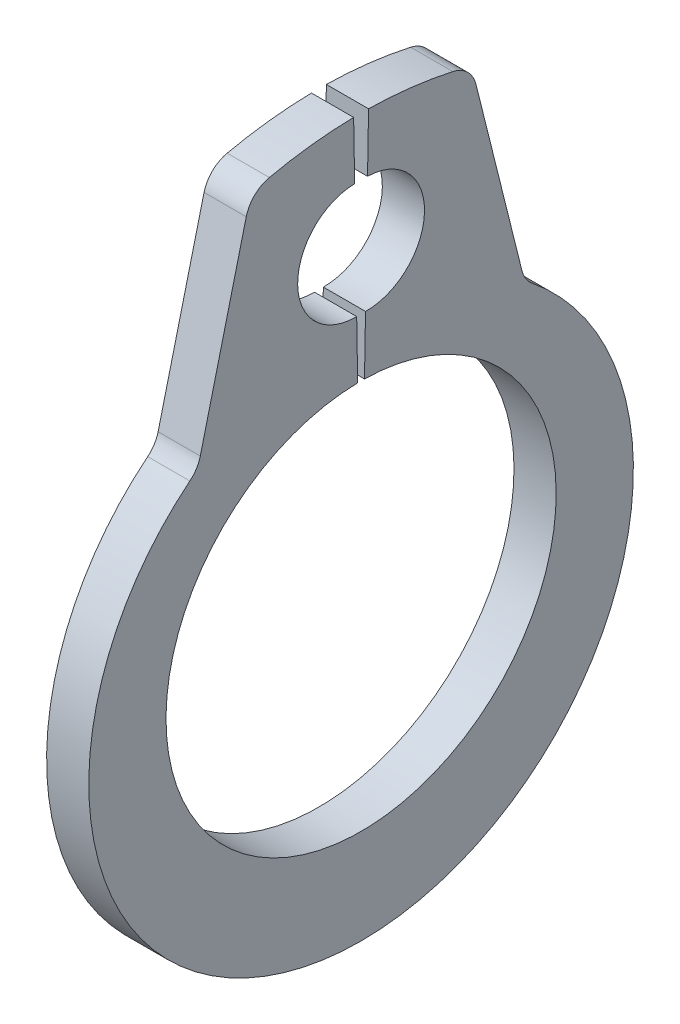
SolidWorks part; units mm, degrees
material "Cast Carbon Steel"
ref_plane "Front" through (0, 0, 0) normal (0, 0, 1) x (1, 0, 0)
ref_plane "Top" through (0, 0, 0) normal (0, 1, 0) x (1, 0, 0)
ref_plane "Right" through (0, 0, 0) normal (1, 0, 0) x (0, 0, -1)
sketch "Sketch1" plane through (0, 0, 0) normal (1, 0, 0) x (0, 0, -1)
  line L0 (0, 0) -> (0, 1.85) construction
  line L1 (-0.0323, 1.8497) -> (-0.0707, 4.0494) construction
  line L2 (-0.0707, 4.0494) -> (-1.0167, 4.0329) construction
  line L3 (-1.0167, 4.0329) -> (-1.549, 1.8982) construction
  line L4 (0.0707, 4.0494) -> (0.0323, 1.8497) construction
  line L5 (0.0707, 4.0494) -> (1.0167, 4.0329) construction
  line L6 (1.0167, 4.0329) -> (1.549, 1.8982) construction
  line L7 (-1.549, 1.8982) -> (-1.1696, 1.4333) construction
  line L8 (1.549, 1.8982) -> (1.1696, 1.4333) construction
  line L9 (0, -1.85) -> (0, -2.75) construction
  line L10 (-1.0167, 4.0329) -> (-0.0323, 1.8497) construction
  line L11 (0.0323, 1.8497) -> (0.0419, 2.3996)
  line L12 (0, 1.85) -> (0, 4.05) construction
  line L13 (1.0468, 3.9124) -> (1.549, 1.8982)
  line L14 (-1.0468, 3.9124) -> (-1.549, 1.8982)
  line L16 (0.0611, 3.4995) -> (0.0707, 4.0494)
  line L17 (-0.0611, 3.4995) -> (-0.0707, 4.0494)
  line L18 (-0.0419, 2.3996) -> (-0.0323, 1.8497)
  circle A0 centre (0, 0) radius 1.85 construction
  arc A1 (-0.0323, 1.8497) -> (0.0323, 1.8497) centre (0, 0) ccw
  circle A2 centre (0, -0.1678) radius 2.5822 construction
  arc A3 (0.0611, 3.4995) -> (0.0419, 2.3996) centre (0.0515, 2.9496) cw
  arc A4 (-0.0419, 2.3996) -> (-0.0611, 3.4995) centre (-0.0515, 2.9496) cw
  arc A6 (-1.549, 1.8982) -> (1.549, 1.8982) centre (0, -0.1678) ccw
  arc A7 (0.0707, 4.0494) -> (1.0468, 3.9124) centre (0, 0) cw
  arc A8 (-0.0707, 4.0494) -> (-1.0468, 3.9124) centre (0, 0) ccw
  dimension "D1" = 75
  dimension "A" = 3.7
  dimension "D2" = 1.1
  dimension "Smin" = 0.6
  dimension "Smax" = 0.9
  dimension "H" = 2.2
  dimension "Angle" = 1
extrude "Extrude1" add sketch "Sketch1" along normal mid plane 0.4
fillet "Fillet1" radius 0.29 4 edges at (0, 1.8982, 1.549) (0, 3.9124, 1.0468) (0, 3.9124, -1.0468) (0, 1.8982, -1.549)
sketch "Sketch2" plane through (0, 0, 0) normal (0, 0, 1) x (1, 0, 0)
  line L0 (-1.25, 0) -> (3.75, 0)
  line L1 (3.75, 0) -> (3.75, -2)
  line L2 (-0.25, -2) -> (-1.15, -2)
  line L3 (3.75, -2) -> (0.25, -2)
  line L4 (0.25, -2) -> (0.25, -1.9)
  line L5 (0.25, -1.9) -> (-0.25, -1.9)
  line L6 (-0.25, -1.9) -> (-0.25, -2)
  line L7 (-0.25, -2) -> (-1.25, -2) construction
  line L8 (-1.25, -2) -> (-1.25, 0) construction
  line L9 (0, -1.9) -> (0, 0) construction
  line L10 (3.75, 0) -> (14.0551, 0) construction
  line L11 (-1.15, -2) -> (-1.25, -1.9)
  line L12 (-1.25, -1.9) -> (-1.25, 0)
  dimension "D1" = 45
  dimension "Dg" = 3.8
  dimension "Ds" = 4
  dimension "D2" = 5
  dimension "W" = 0.5
  dimension "D3" = 1.25
revolve "Revolve1" [suppressed] add sketch "Sketch2" angle 360 about L10
equation "\"D2@Sketch2\" = \"W@Sketch2\"*10"
equation "\"D3@Sketch2\" = \"D2@Sketch2\"/4"
equation "\"Smin@Sketch1\" = \"Smax@Sketch1\"/1.5"
equation "\"D2@Sketch1\" = \"H@Sketch1\"/2"
